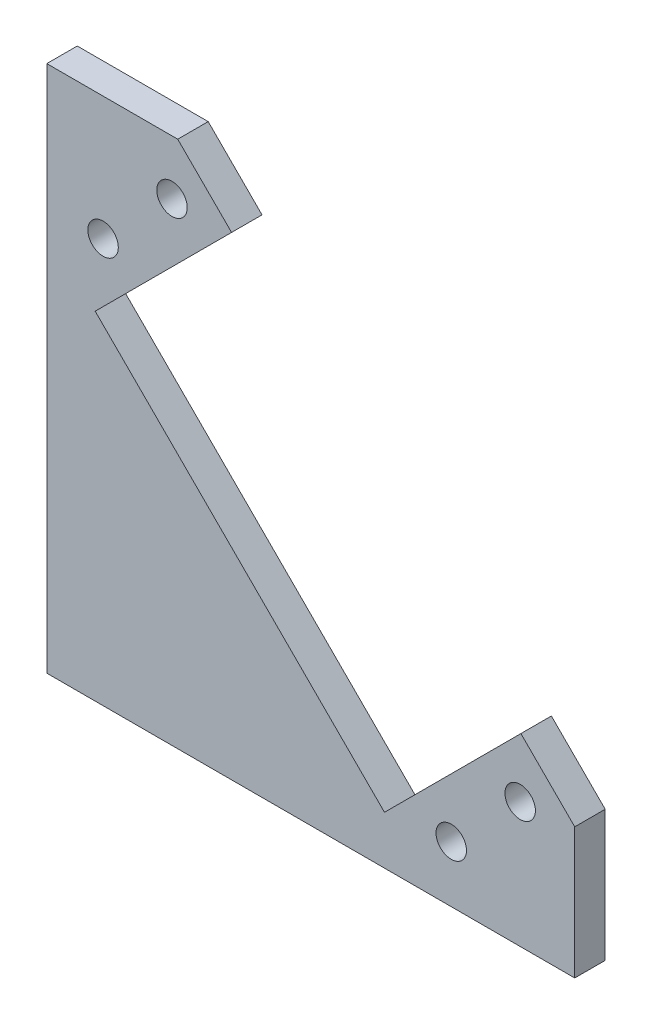
SolidWorks part; units mm, degrees
material "Resina de poliéster"
ref_plane "Alzado" through (0, 0, 0) normal (0, 0, 1) x (1, 0, 0)
ref_plane "Planta" through (0, 0, 0) normal (0, 1, 0) x (1, 0, 0)
ref_plane "Vista lateral" through (0, 0, 0) normal (1, 0, 0) x (0, 0, -1)
sketch "Model" plane through (0, 0, 0) normal (0, 0, 1) x (1, 0, 0)
  line L69 (18.2003, 46.6967) -> (4.7653, 33.2617)
  line L70 (33.2617, 4.7653) -> (4.7653, 33.2617)
  line L71 (0, 52) -> (0, 0)
  line L72 (0, 0) -> (52, 0)
  line L73 (46.6967, 18.2003) -> (33.2617, 4.7653)
  line L74 (0, 52) -> (12.897, 52)
  line L75 (52, 12.897) -> (52, 0)
  line L76 (46.6967, 18.2003) -> (52, 12.897)
  line L77 (18.2003, 46.6967) -> (12.897, 52)
  circle A108 centre (5.5431, 39.8378) radius 1.5
  circle A109 centre (12.3313, 46.626) radius 1.5
  circle A110 centre (46.626, 12.3313) radius 1.5
  circle A111 centre (39.8378, 5.5431) radius 1.5
  dimension "D3" = 3
  dimension "D6" = 9.6
  dimension "D1" = 52
  dimension "D2" = 12.897
  dimension "D4" = 52
  dimension "D5" = 7.5
  dimension "D7" = 40.3
  dimension "D8" = 7.5
  dimension "D9" = 12.897
  dimension "D10" = 19
extrude "Saliente-Extruir2" add sketch "Model" along normal blind 3 contours L69 L77 L74 L71 L72 L75 L76 L73 L70 A111 A110 A109 A108
